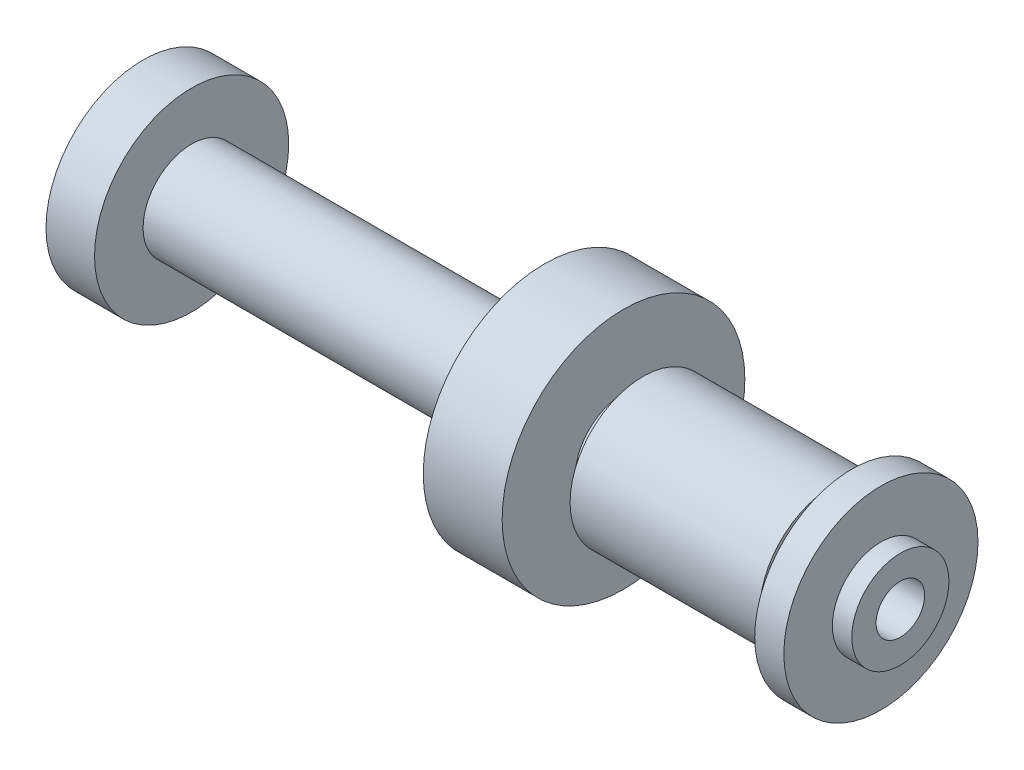
SolidWorks part; units mm, degrees
material "1060-H18 Rod (SS)"
ref_plane "Front Plane" through (0, 0, 0) normal (0, 0, 1) x (1, 0, 0)
ref_plane "Top Plane" through (0, 0, 0) normal (0, 1, 0) x (1, 0, 0)
ref_plane "Right Plane" through (0, 0, 0) normal (1, 0, 0) x (0, 0, -1)
other "Configuration Table"
sketch "Sketch1" plane through (0, 0, 0) normal (0, 0, 1) x (1, 0, 0)
  line L0 (0, 0) -> (88.0533, 0) construction
  line L1 (0, 0) -> (0, 6.35)
  line L2 (0, 6.35) -> (-2.54, 6.35)
  line L3 (-2.54, 6.35) -> (-2.54, 12.7)
  line L4 (-2.54, 12.7) -> (-6.35, 12.7)
  line L5 (-6.35, 12.7) -> (-6.35, 6.35)
  line L6 (-6.35, 6.35) -> (-8.89, 6.35)
  line L7 (-8.89, 6.35) -> (-8.89, 9.525)
  line L8 (-8.89, 9.525) -> (-33.6749, 9.525)
  line L9 (-33.6749, 9.525) -> (-33.6749, 6.35)
  line L10 (-33.6749, 6.35) -> (-36.2149, 6.35)
  line L11 (-36.2149, 6.35) -> (-36.2149, 15.875)
  line L12 (-36.2149, 15.875) -> (-46.5314, 15.875)
  line L13 (-46.5314, 15.875) -> (-46.5314, 6.35)
  line L14 (-46.5314, 6.35) -> (-92.71, 6.35)
  line L15 (-92.71, 6.35) -> (-92.71, 12.7)
  line L16 (-92.71, 12.7) -> (-99.06, 12.7)
  line L17 (-99.06, 12.7) -> (-99.06, 6.35)
  line L18 (-99.06, 6.35) -> (-101.6, 6.35)
  line L19 (-101.6, 6.35) -> (-101.6, 0)
  line L20 (0, 0) -> (-101.6, 0)
  dimension "D1" = 25.4
  dimension "D2" = 12.7
  dimension "D3" = 19.05
  dimension "D4" = 31.75
  dimension "D5" = 12.7
  dimension "D6" = 101.6
  dimension "D7" = 6.35
  dimension "D8" = 3.81
  dimension "D9" = 2.54
  dimension "D10" = 2.54
  dimension "D11" = 12.7
  dimension "D12" = 2.54
  dimension "D13" = 2.54
revolve "Revolve1" add sketch "Sketch1" angle 360 about L0
sketch "Sketch2" plane through (0, 0, 0) normal (1, 0, 0) x (0, 0, -1)
  circle A0 centre (0, 0) radius 3.175
  dimension "D1" = 6.35
extrude "Cut-Extrude1" cut sketch "Sketch2" against normal through all both
equation "\"A\"= 3"
equation "\"B\"= 1"
